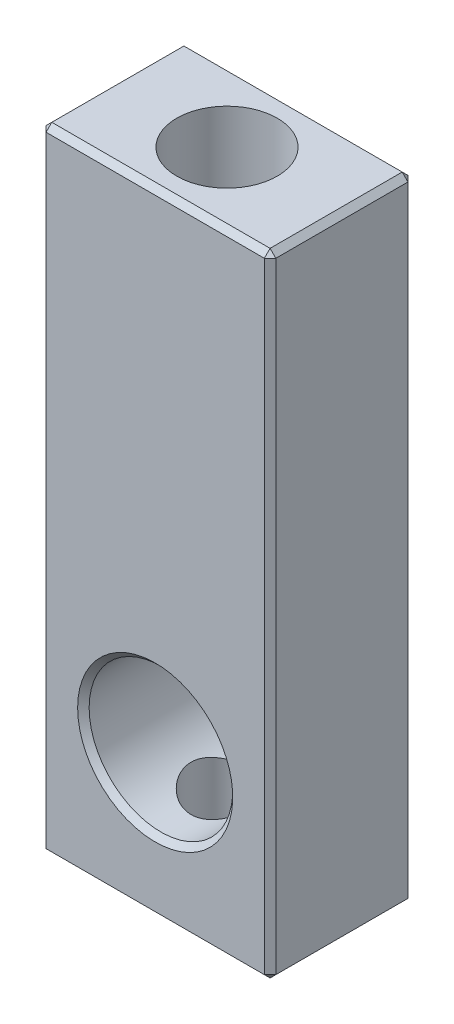
SolidWorks part; units mm, degrees
material "1.0037 (S235JR)"
ref_plane "Vorne" through (0, 0, 0) normal (0, 0, 1) x (1, 0, 0)
ref_plane "Oben" through (0, 0, 0) normal (0, 1, 0) x (1, 0, 0)
ref_plane "Rechts" through (0, 0, 0) normal (1, 0, 0) x (0, 0, -1)
sketch "Skizze1" plane through (0, 0, 0) normal (0, 0, 1) x (1, 0, 0)
  line L1 (-4, -5) -> (4, -5)
  line L2 (-4, -5) -> (-4, 17)
  line L3 (-4, 17) -> (4, 17)
  line L4 (4, -5) -> (4, 17)
  circle A0 centre (0, 0) radius 2.5
  dimension "D4" = 5
  dimension "D1" = 4
  dimension "D2" = 8
  dimension "D3" = 5
  dimension "D5" = 17
extrude "Aufsatz-Linear austragen1" add sketch "Skizze1" along normal blind 5
hole_wizard "M3 Gewindebohrung1" positions "Skizze3" profile "Skizze2" tap size "M3" standard "DIN"
sketch "Skizze3" plane through (0, -5, 0) normal (0, -1, 0) x (-1, 0, 0)
  point P0 (0, -2.5)
  dimension "D1" = 2.5
sketch "Skizze2" plane through (0, -5, 2.5) normal (1, 0, 0) x (0, 0, -1)
  line L0 (0, 0) -> (0, 2.5)
  line L1 (0, 2.5) -> (1.25, 2.5)
  line L2 (1.25, 2.5) -> (1.25, 0)
  line L5 (1.25, 0) -> (0, 0)
  line L11 (0, -6.35) -> (0, 107.95) construction
  dimension "Bohrerdurchmesser" = 2.5
  dimension "Bohrungstiefe" = 2.5
cosmetic thread "Bohrungsgewinde1" parameters "D2"=3
chamfer "Fase1" distance 0.2 angle 45 2 edges at (2.5, 0, 5) (2.5, 0, 0)
chamfer "Fase2" distance 0.2 angle 45 12 edges at (0, 17, 5) (0, 17, 0) (-4, 17, 2.5) (-4, 6, 5) (-4, -5, 2.5) (-4, 6, 0) (4, -5, 2.5) (0, -5, 5) (4, 6, 5) (4, 17, 2.5) (4, 6, 0) (0, -5, 0)
ref_plane "Ebene1" through (0, 6, 0) normal (0, 1, 0) x (1, 0, 0)
sketch "Skizze4" plane through (0, 6, 0) normal (0, 1, 0) x (1, 0, 0)
  circle A0 centre (0, -2.5) radius 1.75
  dimension "D1" = 3.5
  dimension "D2" = 2.5
extrude "Schnitt-Linear austragen1" cut sketch "Skizze4" along normal through all
hole_wizard "M3 Gewindebohrung2" positions "Skizze6" profile "Skizze5" tap size "M3" standard "DIN" end condition up to next
sketch "Skizze6" plane through (0, 6, 0) normal (0, 1, 0) x (1, 0, 0)
  point P0 (0, -2.5)
sketch "Skizze5" plane through (0, 6, 2.5) normal (1, 0, 0) x (0, 0, 1)
  line L0 (0, 0) -> (0, 3.5)
  line L1 (0, 3.5) -> (1.25, 3.5)
  line L2 (1.25, 3.5) -> (1.25, 0)
  line L5 (1.25, 0) -> (0, 0)
  line L11 (0, -6.35) -> (0, 107.95) construction
  dimension "Bohrerdurchmesser" = 2.5
  dimension "Bohrungstiefe" = 3.5
cosmetic thread "Bohrungsgewinde2" parameters "D2"=3
move or copy body "Körper-Verschieben/Kopieren1" [suppressed] bodies to move or copy 104
